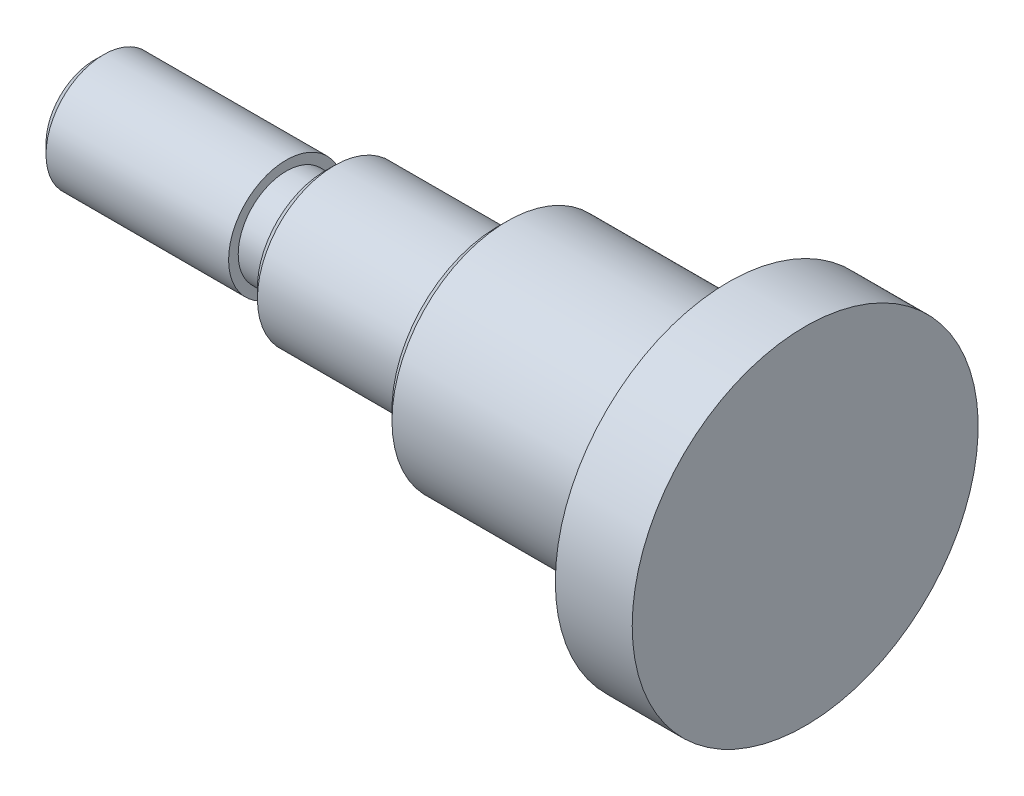
SolidWorks part; units mm, degrees
material "1.0501 (C35)"
ref_plane "Plan de face" through (0, 0, 0) normal (0, 0, 1) x (1, 0, 0)
ref_plane "Plan de dessus" through (0, 0, 0) normal (0, 1, 0) x (1, 0, 0)
ref_plane "Plan de droite" through (0, 0, 0) normal (1, 0, 0) x (0, 0, -1)
sketch "Esquisse1" plane through (0, 0, 0) normal (0, 0, 1) x (1, 0, 0)
  line L0 (0, 0) -> (0, 9)
  line L1 (0, 9) -> (-4, 9)
  line L2 (-4, 9) -> (-4, 6)
  line L3 (-4, 6) -> (-16, 6)
  line L4 (-16, 6) -> (-16, 4)
  line L5 (-16, 4) -> (-25, 4)
  line L6 (-25, 4) -> (-25, 3)
  line L7 (-27, 3) -> (-37, 3)
  line L8 (-37, 3) -> (-37, 0)
  line L9 (-37, 0) -> (0, 0)
  line L10 (-25, 3) -> (-25, 2.5)
  line L11 (-25, 2.5) -> (-27, 2.5)
  line L12 (-27, 2.5) -> (-27, 3)
  dimension "D1" = 4
  dimension "D2" = 12
  dimension "D3" = 9
  dimension "D4" = 12
  dimension "D5" = 9
  dimension "D6" = 6
  dimension "D7" = 4
  dimension "D8" = 3
  dimension "D9" = 2
  dimension "D10" = 2.5
revolve "Révolution1" add sketch "Esquisse1" angle 360 about L9
chamfer "Chanfrein1" distance 0.5 angle 45 1 edges at (-37, 0, 3)
chamfer "Chanfrein2" distance 0.5 angle 45 1 edges at (-16, 0, 6)
chamfer "Chanfrein3" distance 0.5 angle 45 1 edges at (-25, 0, 4)
